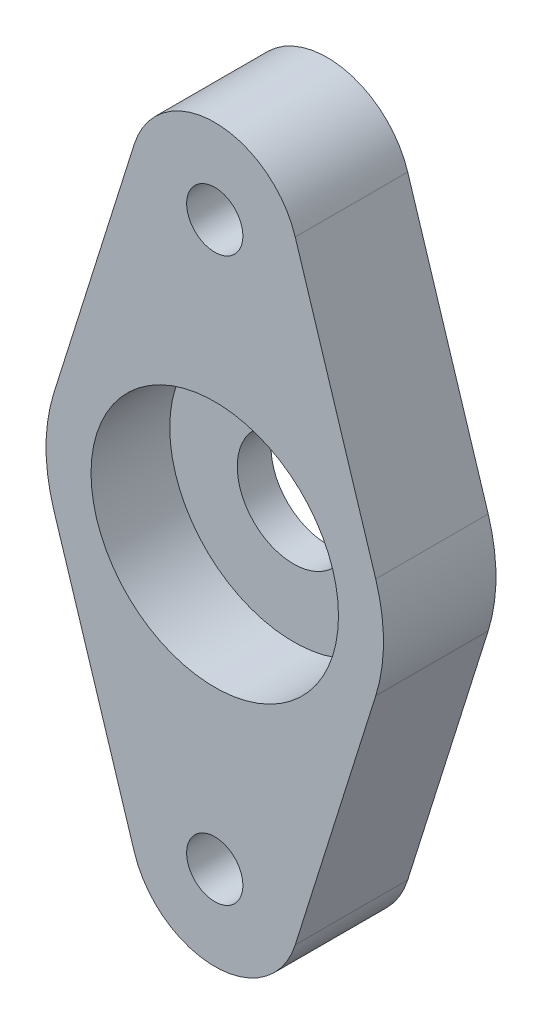
SolidWorks part; units mm, degrees
ref_plane "Спереди" through (0, 0, 0) normal (0, 0, 1) x (1, 0, 0)
ref_plane "Сверху" through (0, 0, 0) normal (0, 1, 0) x (1, 0, 0)
ref_plane "Справа" through (0, 0, 0) normal (1, 0, 0) x (0, 0, -1)
sketch "Эскиз1" plane through (0, 0, 0) normal (0, 0, 1) x (1, 0, 0)
  line L0 (0, 25) -> (0, 0) construction
  line L1 (0, 0) -> (0, -25) construction
  line L2 (-14.3091, 4.5) -> (-7.1545, 27.25)
  line L3 (7.1545, 27.25) -> (14.3091, 4.5)
  line L4 (-14.3091, -4.5) -> (-7.1545, -27.25)
  line L6 (14.3091, -4.5) -> (7.1545, -27.25)
  arc A0 (14.3091, -4.5) -> (14.3091, 4.5) centre (0, 0) ccw
  arc A1 (-14.3091, 4.5) -> (-14.3091, -4.5) centre (0, 0) ccw
  arc A2 (7.1545, 27.25) -> (-7.1545, 27.25) centre (0, 25) ccw
  arc A3 (-7.1545, -27.25) -> (7.1545, -27.25) centre (0, -25) ccw
  circle A4 centre (0, 25) radius 2.5
  circle A5 centre (0, -25) radius 2.5
  point P17 (0, 0)
  dimension "D1" = 30
  dimension "D2" = 15
  dimension "D3" = 15
  dimension "D6" = 5
  dimension "D4" = 25
  dimension "D5" = 25
extrude "Бобышка-Вытянуть1" add sketch "Эскиз1" along normal blind 10
sketch "Эскиз2" plane through (0, 0, 10) normal (0, 0, 1) x (1, 0, 0)
  circle A0 centre (0, 0) radius 11
  dimension "D1" = 22
extrude "Вырез-Вытянуть1" cut sketch "Эскиз2" against normal blind 7
sketch "Эскиз3" plane through (0, 0, 3) normal (0, 0, 1) x (1, 0, 0)
  circle A0 centre (0, 0) radius 5
  dimension "D1" = 10
extrude "Вырез-Вытянуть2" cut sketch "Эскиз3" against normal up to next
